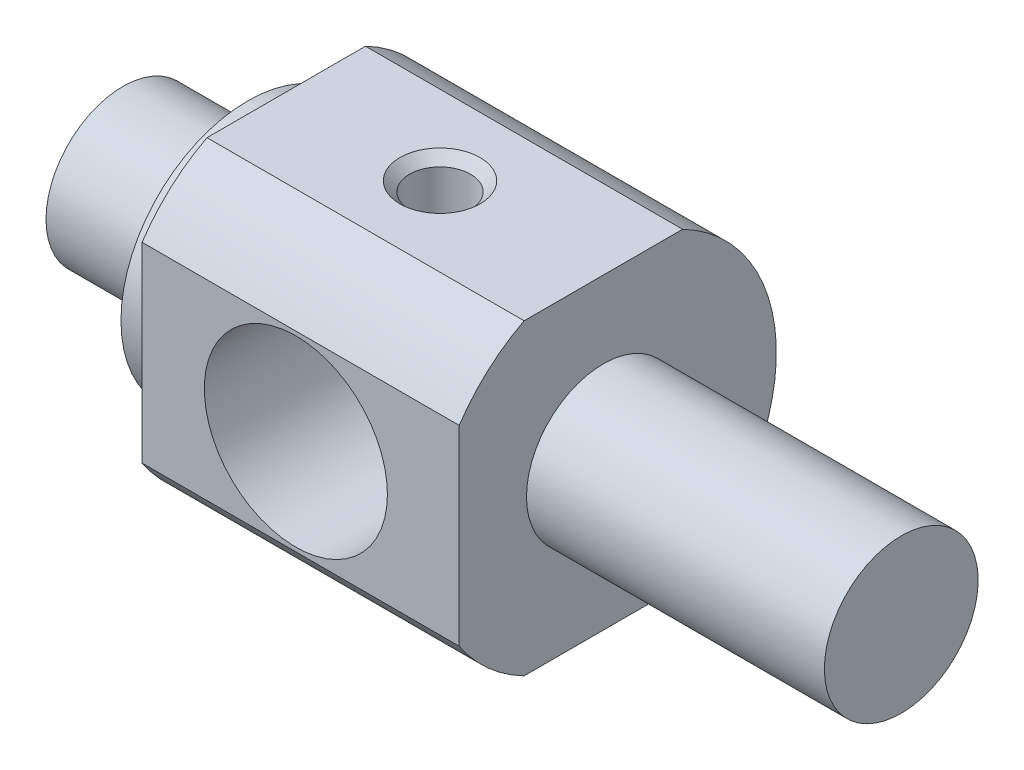
SolidWorks part; units mm, degrees
material "AISI 316 Annealed Stainless Steel Bar (SS)"
ref_plane "Front Plane" through (0, 0, 0) normal (0, 0, 1) x (1, 0, 0)
ref_plane "Top Plane" through (0, 0, 0) normal (0, 1, 0) x (1, 0, 0)
ref_plane "Right Plane" through (0, 0, 0) normal (1, 0, 0) x (0, 0, -1)
sketch "Sketch1" plane through (0, 0, 0) normal (0, 1, 0) x (1, 0, 0)
  line L0 (-16.5, 0) -> (24, 0)
  line L1 (24, 0) -> (24, 4)
  line L2 (24, 4) -> (8.5, 4)
  line L3 (8.5, 4) -> (8.5, 9)
  line L4 (8.5, 9) -> (-10, 9)
  line L5 (-10, 9) -> (-10, 4)
  line L6 (-10, 4) -> (-16.5, 4)
  line L7 (-16.5, 4) -> (-16.5, 0)
  line L8 (0, 0) -> (0, 9) construction
  dimension "D1" = 4
  dimension "D2" = 9
  dimension "D3" = 16.5
  dimension "D4" = 18.5
  dimension "D5" = 10
  dimension "D6" = 24
revolve "Revolve1" add sketch "Sketch1" angle 360 about L0
ref_plane "Plane1" through (0, 0, 9) normal (0, 0, 1) x (1, 0, 0)
sketch "Sketch2" plane through (0, 0, 9) normal (0, 0, 1) x (1, 0, 0)
  line L1 (-10, 6.35) -> (10, 6.35)
  line L2 (-10, 6.35) -> (-10, -6.35)
  line L3 (-10, -6.35) -> (10, -6.35)
  line L4 (10, 6.35) -> (10, -6.35)
  line L5 (-10, 9) -> (-10, -9) construction
  line L6 (-10, 0) -> (0, 0) construction
  line L7 (0, 0) -> (0, -6.35) construction
  dimension "D1" = 12.7
extrude "Cut-Extrude1" cut sketch "Sketch2" against normal blind 1.5 contours L4 L1 L2 L3
hole_wizard "M8x1.25 Tapped Hole1" [suppressed] positions "Sketch3" profile "Sketch4" tap size "M8x1.25" standard "ANSI Metric"
sketch "Sketch3" plane through (0, 0, 11.2) normal (0, 0, 1) x (1, 0, 0)
  point P0 (0, 0)
sketch "Sketch4" plane through (0, 0, 11.2) normal (1, 0, 0) x (0, -1, 0)
  line L0 (0, 0) -> (0, 23.9)
  line L1 (0, 23.9) -> (3.4, 23.9)
  line L2 (3.4, 23.9) -> (3.4, 0)
  line L5 (3.4, 0) -> (0, 0)
  line L11 (0, -6.35) -> (0, 107.95) construction
  dimension "Thru Tap Drill Dia." = 6.8
  dimension "Thru Tap Drill Depth" = 23.9
cosmetic thread "Hole Thread1" [suppressed] parameters "D2"=8
hole_wizard "#8-32 Tapped Hole1" positions "Sketch5" profile "Sketch6" tap size "#8-32" standard "ANSI Inch"
sketch "Sketch5" plane through (-16.5, 0, 0) normal (-1, 0, 0) x (0, 0, 1)
  point P0 (0, 0)
sketch "Sketch6" plane through (-16.5, 0, 0) normal (0, 1, 0) x (0, 0, 1)
  line L0 (0, 0) -> (0, 11.7478)
  line L1 (0, 11.7478) -> (1.7272, 10.71)
  line L2 (1.7272, 10.71) -> (1.7272, 0)
  line L5 (1.7272, 0) -> (0, 0)
  line L10 (0, 11.7478) -> (-1.7272, 10.71) construction
  line L11 (0, -6.35) -> (0, 107.95) construction
  dimension "Tap Drill Dia." = 3.4544
  dimension "Tap Drill Depth" = 10.71
  dimension "Drill Angle" = 118
cosmetic thread "Hole Thread2" parameters "D1"=8.33, "D2"=4.1656
sketch "Sketch7" plane through (-10, 0, 0) normal (-1, 0, 0) x (0, 0, 1)
  circle A0 centre (0, 0) radius 6.6
  dimension "D1" = 13.2
extrude "Cut-Extrude2" cut sketch "Sketch7" against normal blind 2 flip side to cut
sketch "Sketch8" plane through (8.5, 0, 0) normal (1, 0, 0) x (0, 0, -1)
  circle A1 centre (0, 0) radius 6.6
  circle A2 centre (0, 0) radius 6.6
  dimension "D1" = 0
extrude "Cut-Extrude3" [suppressed] cut sketch "Sketch8" against normal blind 1 flip side to cut
hole_wizard "3/8 (0.3750) Dowel Hole2" positions "Sketch9" profile "Sketch10" hole size "3/8" standard "ANSI Inch" end condition through all
sketch "Sketch9" plane through (0, 0, 7.5) normal (0, 0, 1) x (1, 0, 0)
  point P0 (0, 0)
sketch "Sketch10" plane through (0, 0, 7.5) normal (1, 0, 0) x (0, -1, 0)
  line L0 (0, 0) -> (0, 16.5)
  line L1 (0, 16.5) -> (4.7625, 16.5)
  line L2 (4.7625, 16.5) -> (4.7625, 0)
  line L5 (4.7625, 0) -> (0, 0)
  line L11 (0, -6.35) -> (0, 107.95) construction
  dimension "Thru Hole Dia." = 9.525
  dimension "Thru Hole Depth" = 16.5
sketch "Sketch11" plane through (0, 0, 0) normal (0, 1, 0) x (1, 0, 0)
  line L1 (9, -10) -> (-9, -10)
  line L2 (9, -10) -> (9, 10)
  line L3 (9, 10) -> (-9, 10)
  line L4 (-9, -10) -> (-9, 10)
  line L5 (9, -10) -> (-9, 10) construction
  line L6 (9, 10) -> (-9, -10) construction
  circle A0 centre (0, 0) radius 9 construction
  dimension "D1" = 18
  dimension "D2" = 18
  dimension "D3" = 20
extrude "Cut-Extrude4" cut sketch "Sketch11" against normal blind 1 from offset 9
hole_wizard "1/8 (0.1250) Dowel Hole1" positions "Sketch12" profile "Sketch13" hole size "1/8" standard "ANSI Inch" end condition through all
sketch "Sketch12" plane through (0, 8, 0) normal (0, 1, 0) x (1, 0, 0)
  point P0 (0, 0)
sketch "Sketch13" plane through (0, 8, 0) normal (1, 0, 0) x (0, 0, 1)
  line L0 (0, 0) -> (0, 17)
  line L1 (0, 17) -> (1.5875, 17)
  line L2 (1.5875, 17) -> (1.5875, 0)
  line L5 (1.5875, 0) -> (0, 0)
  line L11 (0, -6.35) -> (0, 107.95) construction
  dimension "Thru Hole Dia." = 3.175
  dimension "Thru Hole Depth" = 17
mirror "Mirror1" about plane through (0, 0, 0) normal (0, 1, 0) of "Cut-Extrude4"
chamfer "Chamfer1" distance 0.5 angle 45 1 edges at (0, 8, 1.5875)
